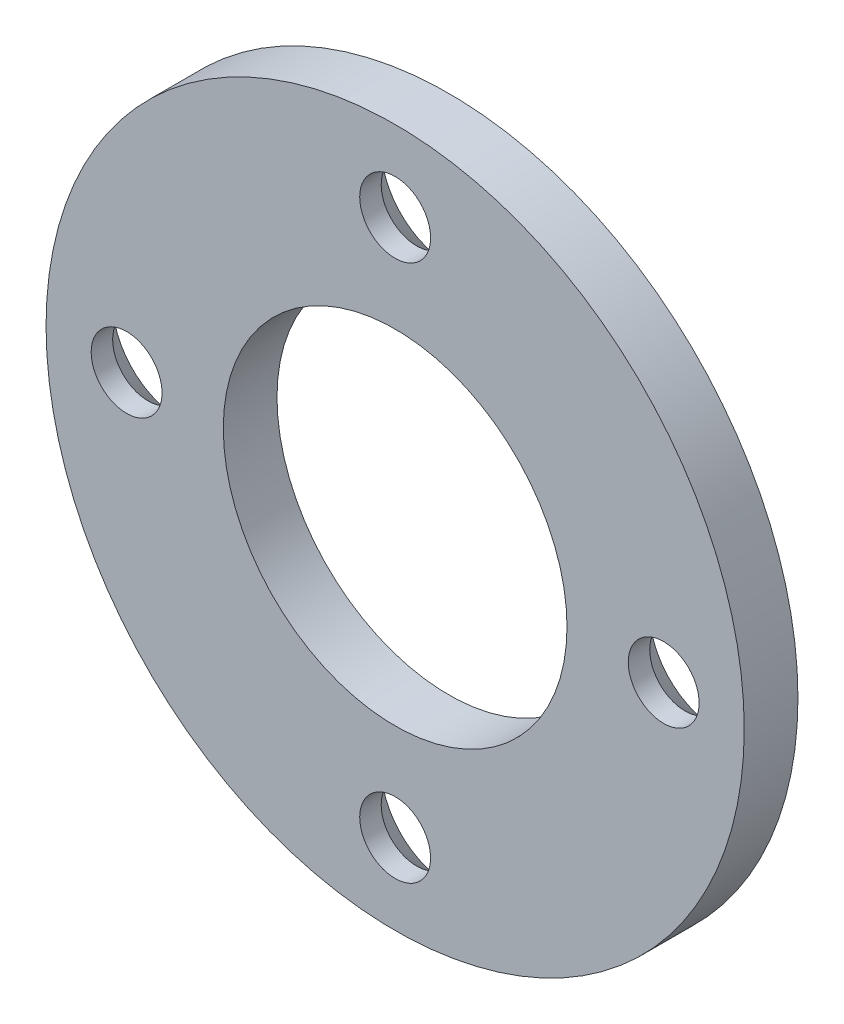
SolidWorks part; units mm, degrees
ref_plane "Plan de face" through (0, 0, 0) normal (0, 0, 1) x (1, 0, 0)
ref_plane "Plan de dessus" through (0, 0, 0) normal (0, 1, 0) x (1, 0, 0)
ref_plane "Plan de droite" through (0, 0, 0) normal (1, 0, 0) x (0, 0, -1)
sketch "Esquisse1" plane through (0, 0, 0) normal (0, 0, 1) x (1, 0, 0)
  circle A0 centre (0, 0) radius 32.5
  dimension "D1" = 65
extrude "Boss.-Extru.1" add sketch "Esquisse1" along normal blind 5
sketch "Esquisse2" plane through (0, 0, 5) normal (0, 0, 1) x (1, 0, 0)
  circle A0 centre (0, 0) radius 17 construction
  circle A1 centre (0, 0) radius 16
  dimension "D1" = 32
  dimension "D2" = 34
hole_wizard "Fraisage pour vis à tête fraisée M61" positions "Esquisse6" profile "Esquisse5" countersink size "M6" standard "ISO" end condition through all
sketch "Esquisse6" plane through (0, 0, 0) normal (0, 0, -1) x (-1, 0, 0)
  circle A2 centre (0, 0) radius 25
  point P9 (0, -25)
  dimension "D1" = 50
sketch "Esquisse5" plane through (0, -25, 0) normal (1, 0, 0) x (0, 1, 0)
  line L0 (0, 0) -> (0, 5)
  line L1 (0, 5) -> (3.3, 5)
  line L2 (3.3, 5) -> (3.3, 3)
  line L3 (3.3, 3) -> (6.3, 0)
  line L5 (6.3, 0) -> (0, 0)
  line L6 (-3.3, 3) -> (-6.3, 0) construction
  line L11 (0, -6.35) -> (0, 107.95) construction
  dimension "Diamètre du perçage jusqu'au prochain" = 6.6
  dimension "Profondeur du perçage jusqu'au prochain" = 5
  dimension "Diamètre du fraisage entrant" = 12.6
  dimension "Angle du fraisage entrant" = 90
pattern_circular "Répétition circulaire1" count 4 over 360 about axis through (0, 0, 0) along (0, 0, 1) of "Fraisage pour vis à tête fraisée M61"
extrude "Enlèv. mat.-Extru.1" cut sketch "Esquisse2" against normal through all
